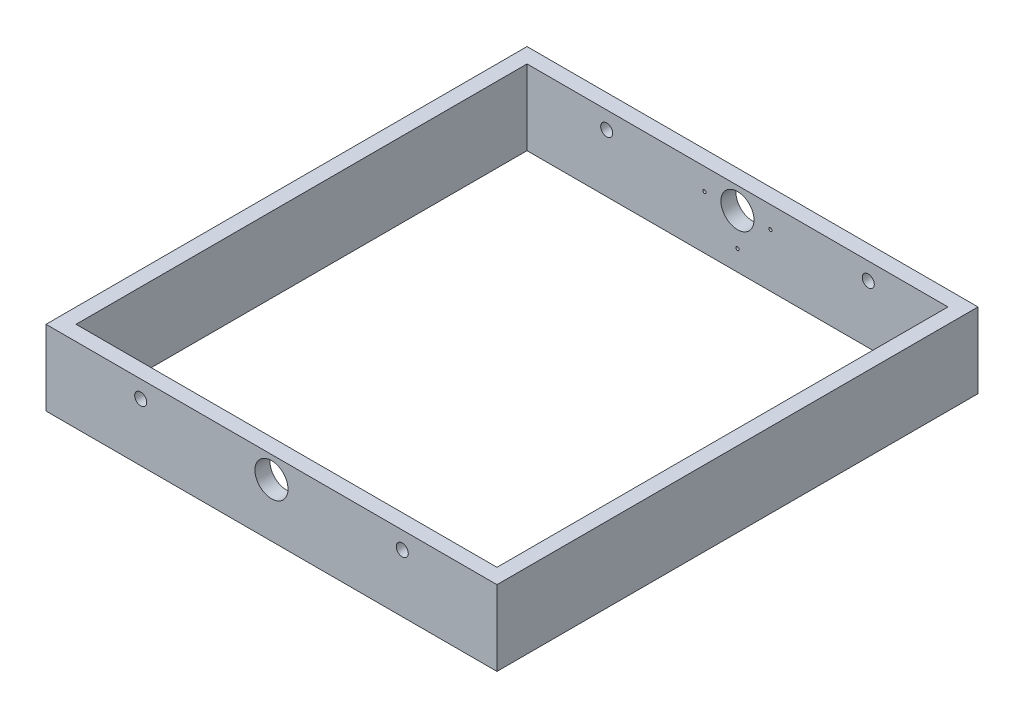
SolidWorks part; units mm, degrees
ref_plane "Alzado" through (0, 0, 0) normal (0, 0, 1) x (1, 0, 0)
ref_plane "Planta" through (0, 0, 0) normal (0, 1, 0) x (1, 0, 0)
ref_plane "Vista lateral" through (0, 0, 0) normal (1, 0, 0) x (0, 0, -1)
sketch "Croquis1" plane through (0, 0, 0) normal (0, 1, 0) x (1, 0, 0)
  line L1 (-150, -160) -> (150, -160)
  line L2 (-150, -160) -> (-150, 160)
  line L3 (-150, 160) -> (150, 160)
  line L4 (150, -160) -> (150, 160)
  line L5 (-150, -160) -> (150, 160) construction
  line L6 (-150, 160) -> (150, -160) construction
  line L11 (-140, 150) -> (140, 150)
  line L12 (-140, 150) -> (-140, -150)
  line L13 (-140, -150) -> (140, -150)
  line L14 (140, 150) -> (140, -150)
  line L15 (-140, 150) -> (140, -150) construction
  line L16 (-140, -150) -> (140, 150) construction
  point P0 (0, 0)
  point P6 (0, 0)
  point P7 (0, 0)
  dimension "D1" = 320
  dimension "D2" = 300
  dimension "D3" = 280
  dimension "D4" = 300
extrude "Saliente-Extruir1" add sketch "Croquis1" along normal blind 50
sketch "Croquis2" plane through (0, 0, 160) normal (0, 0, 1) x (1, 0, 0)
  line L0 (-91, 38.5) -> (91, 38.5) construction
  line L3 (0, 50) -> (0, 0) construction
  line L4 (-150, 50) -> (150, 50) construction
  line L5 (-87, 50) -> (-87, 0) construction
  line L6 (87, 50) -> (87, 0) construction
  circle A0 centre (-87, 38.5) radius 4
  circle A1 centre (0, 35.5) radius 11
  circle A2 centre (87, 38.5) radius 4
  point P1 (0, 0)
  point P2 (0, 27.2382)
  dimension "D3" = 8
  dimension "D4" = 8
  dimension "D5" = 22
  dimension "D7" = 3
  dimension "D6" = 11.5
  dimension "D1" = 87
  dimension "D2" = 87
extrude "Cortar-Extruir1" cut sketch "Croquis2" against normal through all
sketch "Croquis3" plane through (0, 50, 0) normal (0, 1, 0) x (1, 0, 0)
  line L4 (150, -160) -> (150, 160)
  line L5 (150, 160) -> (-150, 160)
  line L6 (-150, 160) -> (-150, -160)
  line L7 (-150, -160) -> (150, -160)
  line L8 (150, -160) -> (150, 160)
  line L9 (150, 160) -> (-150, 160)
  line L10 (-150, 160) -> (-150, -160)
  line L11 (-150, -160) -> (150, -160)
  dimension "D1" = 0
extrude "Cortar-Extruir2" [suppressed] cut sketch "Croquis3" against normal blind 15
sketch "Sketch1" plane through (0, 0, -160) normal (0, 0, -1) x (-1, 0, 0)
  circle A0 centre (0, 13.5797) radius 1.09
  circle A1 centre (-21.9203, 35.5) radius 1.09
  circle A2 centre (21.9203, 35.5) radius 1.09
  dimension "D1" = 2.18
  dimension "D2" = 2.18
  dimension "D3" = 2.18
extrude "Cut-Extrude1" cut sketch "Sketch1" against normal up to surface (10 mm away) up to face at (-83, 38.5, -150)
